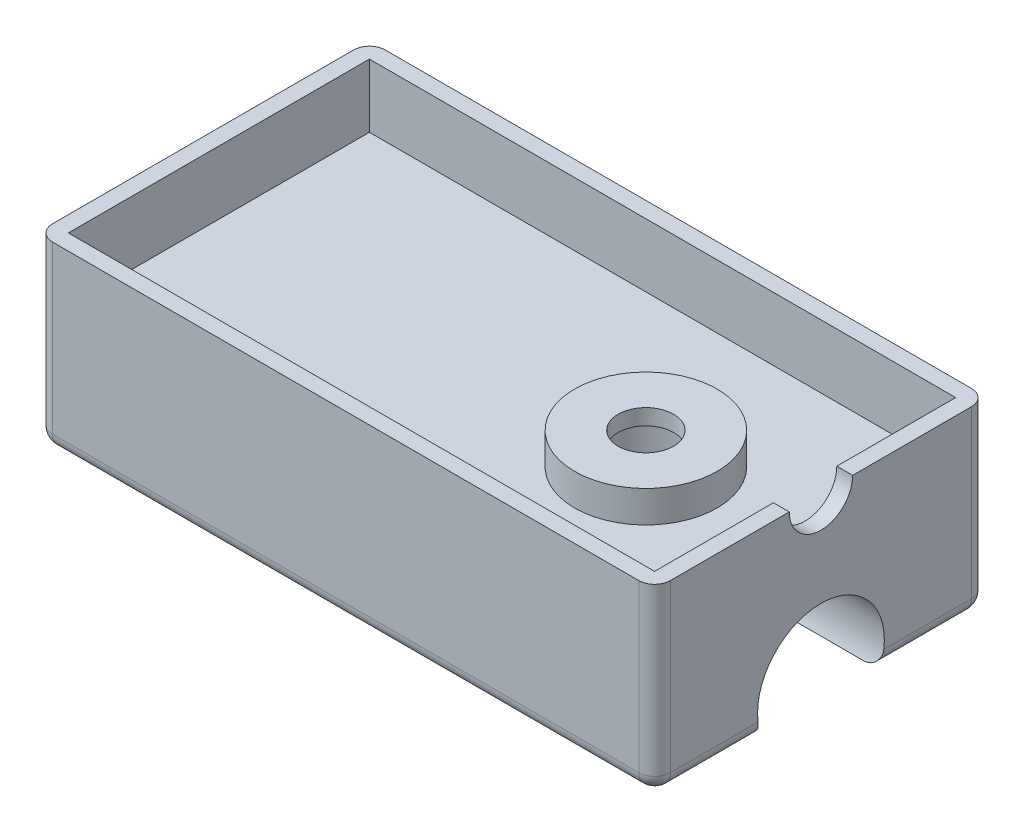
SolidWorks part; units mm, degrees
ref_plane "Front Plane" through (0, 0, 0) normal (0, 0, 1) x (1, 0, 0)
ref_plane "Top Plane" through (0, 0, 0) normal (0, 1, 0) x (1, 0, 0)
ref_plane "Right Plane" through (0, 0, 0) normal (1, 0, 0) x (0, 0, -1)
sketch "Sketch1" plane through (0, 0, 0) normal (0, 1, 0) x (1, 0, 0)
  line L1 (0, 0) -> (39, 0)
  line L2 (0, 0) -> (0, 21)
  line L3 (0, 21) -> (39, 21)
  line L4 (39, 0) -> (39, 21)
  dimension "D1" = 39
  dimension "D2" = 21
extrude "Boss-Extrude1" add sketch "Sketch1" along normal blind 11.5
sketch "Sketch3" plane through (0, 11.5, 0) normal (0, 1, 0) x (1, 0, 0)
  line L8 (1, 20) -> (1, 1)
  line L9 (1, 1) -> (38, 1)
  line L10 (38, 1) -> (38, 20)
  line L11 (38, 20) -> (1, 20)
  line L12 (1, 20) -> (1, 1)
  line L13 (1, 1) -> (38, 1)
  line L14 (38, 1) -> (38, 20)
  line L15 (38, 20) -> (1, 20)
  dimension "D1" = 1
extrude "Cut-Extrude2" cut sketch "Sketch3" against normal blind 4
sketch "Sketch4" plane through (0, 0, 0) normal (-1, 0, 0) x (0, 0, 1)
  line L0 (-10.5, 1.5) -> (-10.5, 0) construction
  line L2 (-21, 0) -> (0, 0) construction
  line L4 (-21, 11.5) -> (0, 11.5) construction
  line L6 (-10.5, 5.5) -> (-10.5, 11.5) construction
  line L7 (-14.2081, 0) -> (-6.7919, 0) construction
  line L8 (-14.2081, 0) -> (-6.7919, 0)
  arc A1 (-6.7919, 0) -> (-14.2081, 0) centre (-10.5, 1.5) ccw
  dimension "D2" = 6
  dimension "D1" = 8
  dimension "D3" = 7.4162
fillet "Fillet1" radius 1 4 edges at (0, 5.75, 0) (39, 5.75, 0) (39, 5.75, -21) (0, 5.75, -21)
fillet "Fillet2" radius 1 8 edges at (0, 0, -10.5) (0.2929, 0, -0.2929) (19.5, 0, 0) (38.7071, 0, -0.2929) (39, 0, -10.5) (0.2929, 0, -20.7071) (38.7071, 0, -20.7071) (19.5, 0, -21)
sketch "Sketch5" plane through (0, 7.5, 0) normal (0, 1, 0) x (1, 0, 0)
  line L0 (1, 20) -> (1, 1) construction
  line L1 (38, 1) -> (38, 20) construction
  line L2 (1, 1) -> (38, 1) construction
  line L3 (38, 20) -> (1, 20) construction
  circle A0 centre (28.01, 10.44) radius 4.5
  dimension "D5" = 9
  dimension "D1" = 27.01
  dimension "D2" = 9.99
  dimension "D3" = 9.44
  dimension "D4" = 9.56
extrude "Boss-Extrude2" add sketch "Sketch5" along normal blind 2
sketch "Sketch6" plane through (0, 9.5, 0) normal (0, 1, 0) x (1, 0, 0)
  circle A2 centre (28.01, 10.44) radius 3.5
  circle A3 centre (28.01, 10.44) radius 3.5
  dimension "D1" = 1
extrude "Cut-Extrude4" cut sketch "Sketch6" against normal up to surface (9.5 mm away) up to face at (19.5, 0, -10.5)
sketch "Sketch7" plane through (0, 9.5, 0) normal (0, 1, 0) x (1, 0, 0)
  circle A1 centre (28.01, 10.44) radius 4.5
  circle A2 centre (28.01, 10.44) radius 4.5
  dimension "D1" = 0
extrude "Boss-Extrude3" add sketch "Sketch7" against normal blind 1
sketch "Sketch8" plane through (0, 9.5, 0) normal (0, 1, 0) x (1, 0, 0)
  circle A0 centre (28.01, 10.44) radius 1.75
  dimension "D1" = 3.5
extrude "Cut-Extrude5" cut sketch "Sketch8" against normal up to surface (1 mm away) up to face at (28.01, 8.5, -6.94)
sketch "Sketch9" plane through (39, 0, 0) normal (1, 0, 0) x (0, 0, -1)
  line L0 (1, 11.5) -> (20, 11.5) construction
  line L1 (8.5, 11.5) -> (12.5, 11.5)
  arc A0 (8.5, 11.5) -> (12.5, 11.5) centre (10.5, 11.5) ccw
  dimension "D1" = 4
extrude "Cut-Extrude6" cut sketch "Sketch9" against normal up to surface (1 mm away) up to face at (38, 9.5, -10.5)
extrude "Cut-Extrude7" cut sketch "Sketch4" against normal up to surface (39 mm away) up to face at (39, 7.6667, -10.5)
